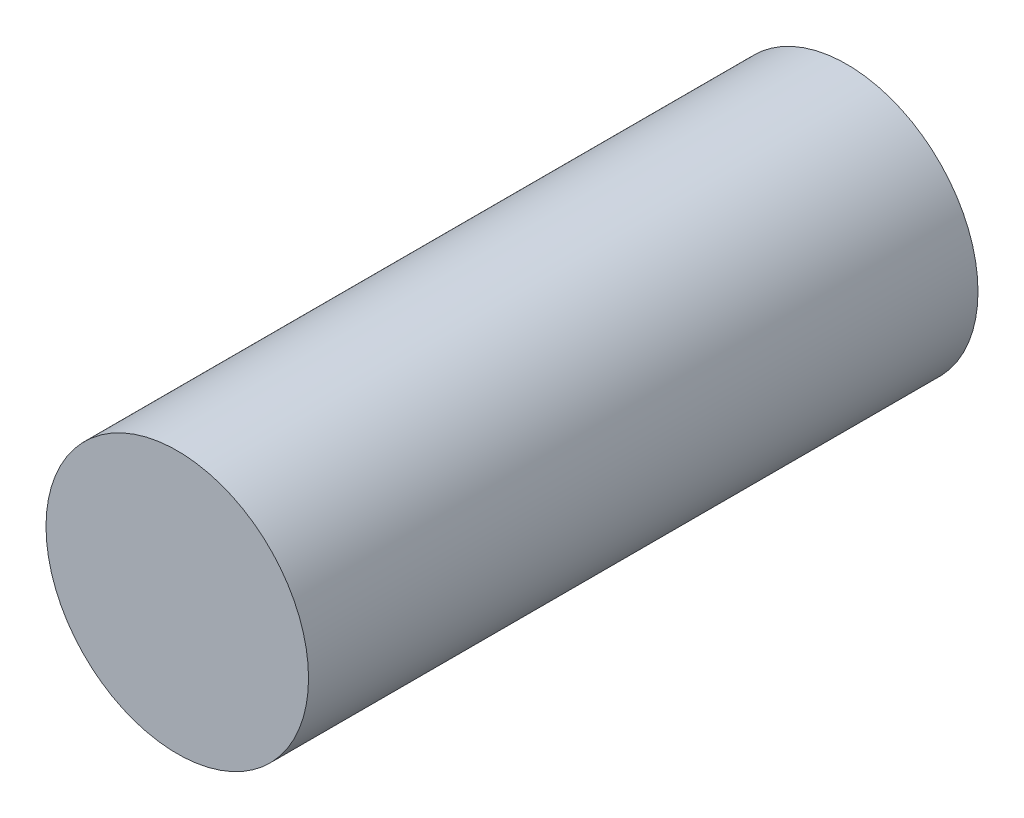
SolidWorks part; units mm, degrees
ref_plane "Front Plane" through (0, 0, 0) normal (0, 0, 1) x (1, 0, 0)
ref_plane "Top Plane" through (0, 0, 0) normal (0, 1, 0) x (1, 0, 0)
ref_plane "Right Plane" through (0, 0, 0) normal (1, 0, 0) x (0, 0, -1)
sketch "Sketch1" plane through (0, 0, 0) normal (0, 0, 1) x (1, 0, 0)
  circle A0 centre (0, 0) radius 13
  dimension "D1" = 26
extrude "Boss-Extrude1" add sketch "Sketch1" along normal blind 66.3
